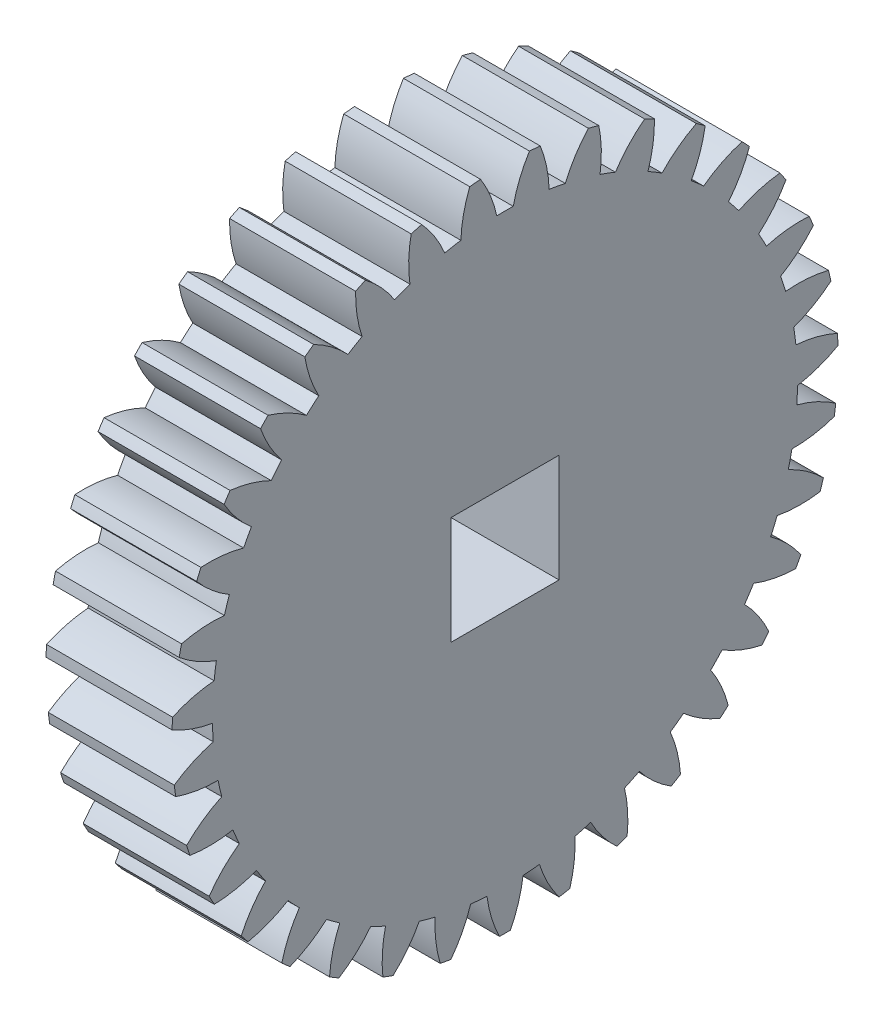
SolidWorks part; units mm, degrees
ref_plane "Plane1" through (0, 0, 0) normal (0, 0, 1) x (1, 0, 0)
ref_plane "Plane2" through (0, 0, 0) normal (0, 1, 0) x (1, 0, 0)
ref_plane "Plane3" through (0, 0, 0) normal (1, 0, 0) x (0, 0, -1)
sketch "HoldingSke" plane through (0, 0, 0) normal (0, 1, 0) x (1, 0, 0)
  line L0 (0, 0) -> (0.8192, -0.5736)
  line L1 (-15, 0) -> (100, 0) construction
  line L2 (0, 0) -> (-2.1039, 2.3779)
  line L3 (0, 0) -> (-11.863, 4.5341)
  line L4 (0, 0) -> (7.0742, 4.9534)
  line L5 (0, 0) -> (-46.8476, -17.4728)
  line L6 (0, 0) -> (-4.1448, -2.7965)
  line L7 (-2.1039, 2.3779) -> (8.6587, 51.2062)
  line L8 (-76.2, 54.61) -> (-75.2, 54.61)
  line L9 (-71.009, 38.7566) -> (-53.1078, 45.2721)
  line L10 (-76.2, 71.12) -> (104.1128, 71.12)
  line L11 (0, 0) -> (-5, 0)
  line L12 (-76.2, 101.6) -> (-76.162, 101.6)
  line L13 (24.9733, 27.94) -> (52.9518, 28.4284)
  line L14 (24.9733, 27.94) -> (24.9743, 27.94)
  line L15 (24.9733, 27.94) -> (100.4006, 29.5858)
  line L16 (-63.627, -1) -> (-12.827, -1)
  circle A0 centre (0, 0) radius 3
  circle A1 centre (0, 0) radius 16.249
  circle A2 centre (0, 0) radius 37.5
  circle A3 centre (0, 0) radius 3
  dimension "MHD" = 32.498
  dimension "Hub_dia" = 75
  dimension "Bore" = 6
  dimension "MBD" = 6
  dimension "Num_teeth" = 35
  dimension "Pitch_radius" = 180.3128
  dimension "Pitch" = 1
  dimension "Width" = 5
  dimension "Overall_len" = 50
  dimension "Show_teeth" = 35
  dimension "Thickness" = 5
  dimension "OAL" = 50.0004
  dimension "T_dim" = 1
  dimension "Ap" = 20
  dimension "H" = 19.05
  dimension "Backlash" = 0.038
  dimension "Addendum_fac" = 1
  dimension "Dedendum_fac" = 1.25
  dimension "Clearance_fac" = 0.25
  dimension "Dedendum_add" = 0.001
  dimension "Module" = 1
sketch "BasProSke" plane through (0, 0, 0) normal (0, 1, 0) x (1, 0, 0)
  line L0 (-10, 0) -> (60, 0) construction
  line L1 (0, 0) -> (0, 18.5)
  line L2 (0, 0) -> (7, 0)
  line L3 (7, 0) -> (7, 18.5)
  line L4 (7, 18.5) -> (0, 18.5)
  dimension "Diameter" = 37
  dimension "Thickness" = 7
revolve "Base-Revolve" add sketch "BasProSke" angle 360 about L0
sketch "TooCutSke" plane through (0, 0, 0) normal (1, 0, 0) x (0, 0, -1)
  line L1 (0, 0) -> (0, 107) construction
  line L2 (0, 0) -> (-0.8516, 17.4793) construction
  line L3 (0, 0) -> (-3.1347, 34.8297) construction
  line L4 (-0.8516, 17.4793) -> (-1.5674, 17.4148) construction
  arc A0 (0.4564, 16.2426) -> (-0.4564, 16.2426) centre (0, 0) ccw
  arc A1 (1.373, 18.4745) -> (-1.373, 18.4745) centre (0, 0) ccw
  circle A2 centre (0, 0) radius 17.5 construction
  circle A3 centre (0, 0) radius 16.4446 construction
  arc A4 (-0.4564, 16.2426) -> (-1.373, 18.4745) centre (-7.293, 14.739) ccw
  arc A5 (1.373, 18.4745) -> (0.4564, 16.2426) centre (7.293, 14.739) ccw
  dimension "Root_dia" = 32.498
  dimension "Overcut_dia" = 37.0508
  dimension "Pitch_dia" = 35
  dimension "Base_dia" = 32.8892
  dimension "Flank_rad" = 7
  dimension "Half_ang" = 5.143
  dimension "Half_CT" = 0.7186
extrude "ToothCut" cut sketch "TooCutSke" along normal through all
fillet "Breaks" [suppressed] radius 0.02
fillet "RootFillets" [suppressed] radius 0.251
pattern_circular "TeethCuts" count 35 every 10.286 about axis through (-10, 0, 0) along (1, 0, 0) of "ToothCut", "RootFillets", "Breaks"
sketch "HubNeaOneSke" plane through (0, 0, 0) normal (-1, 0, 0) x (0, 0, 1)
  circle A0 centre (0, 0) radius 16.249
  dimension "Diameter" = 32.498
extrude "HubNearOne" [suppressed] add sketch "HubNeaOneSke" along normal blind 43.0004
sketch "HubNeaBotSke" plane through (0, 0, 0) normal (-1, 0, 0) x (0, 0, 1)
  circle A0 centre (0, 0) radius 16.249
  dimension "Diameter" = 32.498
extrude "HubNearBoth" [suppressed] add sketch "HubNeaBotSke" along normal blind 21.5002
ref_plane "FarPln" through (7, 0, 0) normal (1, 0, 0) x (0, 0, -1)
sketch "HubFarSke" plane through (7, 0, 0) normal (1, 0, 0) x (0, 0, -1)
  circle A0 centre (0, 0) radius 16.249
  dimension "Diameter" = 32.498
extrude "HubFar" [suppressed] add sketch "HubFarSke" along normal blind 21.5002
sketch "BorSke" plane through (0, 0, 0) normal (1, 0, 0) x (0, 0, -1)
  circle A0 centre (0, 0) radius 1.5
  dimension "Diameter" = 3
extrude "Bore" cut sketch "BorSke" along normal mid plane 100.0007
sketch "KeySke" plane through (0, 0, 0) normal (1, 0, 0) x (0, 0, -1)
  line L0 (-1, 0) -> (-1, 4)
  line L1 (-1, 4) -> (1, 4)
  line L2 (1, 4) -> (1, 0)
  line L3 (0, 0) -> (0, 34) construction
  line L4 (-1, 0) -> (1, 0)
  dimension "Offset" = 4
  dimension "Width" = 2
extrude "Keyway" [suppressed] cut sketch "KeySke" along normal mid plane 100.0007
pattern_circular "Keyway2" [suppressed] count 2 every 90 about axis through (-10, 0, 0) along (1, 0, 0)
sketch "Sketch1" plane through (7, 0, 0) normal (1, 0, 0) x (0, 0, -1)
  line L1 (-3, -3) -> (3, -3)
  line L2 (-3, -3) -> (-3, 3)
  line L3 (-3, 3) -> (3, 3)
  line L4 (3, -3) -> (3, 3)
  line L5 (-3, -3) -> (3, 3) construction
  line L6 (-3, 3) -> (3, -3) construction
  circle A0 centre (0, 0) radius 1.5 construction
  point P0 (0, 0)
  dimension "D1" = 0
  dimension "D2" = 6
  dimension "D3" = 6
extrude "Cut-Extrude1" cut sketch "Sketch1" against normal blind 10
equation "' \"Module@HoldingSke\" = 6.35"
equation "' \"Num_teeth@HoldingSke\" = 12"
equation "' \"Ap@HoldingSke\" =  20"
equation "' \"Width@HoldingSke\" = 0.5 * 25.4"
equation "' \"Hub_dia@HoldingSke\"= 1 * 25.4"
equation "' \"Overall_len@HoldingSke\" = 1.0 * 25.4"
equation "' \"Bore@HoldingSke\" = 0.75 * 25.4"
equation "' \"T_dim@HoldingSke\" = 0.1 * 25.4"
equation "' \"Width@KeySke\" = 0.25 * 25.4"
equation "' \"Show_teeth@HoldingSke\" = 13"
equation "' \"Backlash@HoldingSke\" = 0.009 * 25.4"
equation "' \"Addendum_fac@HoldingSke\" = 1.0"
equation "' \"Dedendum_fac@HoldingSke\" = 1.25"
equation "' \"Dedendum_add@HoldingSke\" = 0.00005 * 25.4"
equation "' \"Clearance_fac@HoldingSke\" = 0.25"
equation "\"Pitch@HoldingSke\" = 1 / \"Module@HoldingSke\""
equation "\"Overcut_dia@TooCutSke\" = (\"Num_teeth@HoldingSke\" + 2 * \"Addendum_fac@HoldingSke\") / \"Pitch@HoldingSke\" + 0.002 * 25.4"
equation "\"Pitch_dia@TooCutSke\" = \"Num_teeth@HoldingSke\" / \"Pitch@HoldingSke\""
equation "\"Base_dia@TooCutSke\" = \"Num_teeth@HoldingSke\" / \"Pitch@HoldingSke\" * cos((\"Ap@HoldingSke\"  * 3.14159265 / 180))"
equation "\"Root_dia@TooCutSke\" = (\"Num_teeth@HoldingSke\" + 2) / \"Pitch@HoldingSke\" - 2 * (\"Addendum_fac@HoldingSke\" + \"Dedendum_fac@HoldingSke\") / \"Pitch@HoldingSke\" - \"Dedendum_add@HoldingSke\" * 2"
equation "\"Half_ang@TooCutSke\" = 180 / \"Num_teeth@HoldingSke\""
equation "\"Half_CT@TooCutSke\" = \"Num_teeth@HoldingSke\" / \"Pitch@HoldingSke\" * sin((3.14159265 / 2 / \"Num_teeth@HoldingSke\")) / 2 - 7 * \"Backlash@HoldingSke\" / 4"
equation "\"Flank_rad@TooCutSke\" = \"Num_teeth@HoldingSke\" / \"Pitch@HoldingSke\" / 5"
equation "\"Radius@RootFillets\" = \"Clearance_fac@HoldingSke\" / \"Pitch@HoldingSke\" + \"Dedendum_add@HoldingSke\""
equation "\"Break_rad@Breaks\" = 0.02 / \"Pitch@HoldingSke\""
equation "\"Thickness@HoldingSke\" = \"Width@HoldingSke\""
equation "\"OAL@HoldingSke\" = \"Thickness@HoldingSke\""
equation "\"MHD@HoldingSke\" = (\"Num_teeth@HoldingSke\" + 2) / \"Pitch@HoldingSke\" - 2 * (\"Addendum_fac@HoldingSke\" + \"Dedendum_fac@HoldingSke\")  / \"Pitch@HoldingSke\" - \"Dedendum_add@HoldingSke\" * 2"
equation "\"MBD@HoldingSke\" = (\"Num_teeth@HoldingSke\" + 2) / \"Pitch@HoldingSke\" - 2 * (\"Addendum_fac@HoldingSke\" + \"Dedendum_fac@HoldingSke\")  / \"Pitch@HoldingSke\" - \"Dedendum_add@HoldingSke\" * 2 - 0.002 * 25.4"
equation "\"MHD@HoldingSke\" = ((sgn( \"MHD@HoldingSke\" - \"Hub_dia@HoldingSke\" )-1)*( \"MHD@HoldingSke\" - \"Hub_dia@HoldingSke\" ))/-2+ \"Hub_dia@HoldingSke\""
equation "\"MBD@HoldingSke\" = ((sgn( \"MBD@HoldingSke\" - \"Bore@HoldingSke\" )-1)*( \"MBD@HoldingSke\" - \"Bore@HoldingSke\" ))/-2+ \"Bore@HoldingSke\""
equation "\"OAL@HoldingSke\" = ((sgn( \"OAL@HoldingSke\" - \"Overall_len@HoldingSke\" )+1)*( \"OAL@HoldingSke\" - \"Overall_len@HoldingSke\" ))/2 + \"Overall_len@HoldingSke\" + 0.000002 * 25.4"
equation "\"Num_teeth@TeethCuts\" = int( \"Show_teeth@HoldingSke\" ) + 1"
equation "\"Num_teeth@TeethCuts\" = ((sgn( \"Num_teeth@TeethCuts\" - \"Num_teeth@HoldingSke\" )-1)*( \"Num_teeth@TeethCuts\" - \"Num_teeth@HoldingSke\" ))/-2+ \"Num_teeth@HoldingSke\""
equation "\"Num_teeth@TeethCuts\" = ((sgn( \"Num_teeth@TeethCuts\" - 2.0)+1)*( \"Num_teeth@TeethCuts\" - 2.0))/2 +2.0"
equation "\"Angle@TeethCuts\" = 360.0 / \"Num_teeth@HoldingSke\""
equation "\"Diameter@BasProSke\" = (\"Num_teeth@HoldingSke\" + 2 * \"Addendum_fac@HoldingSke\") / \"Pitch@HoldingSke\""
equation "\"Thickness@BasProSke\"=7mm"
equation "' \"Fillet_rad@BasProSke\" =  \"Thickness@HoldingSke\" * 0.05"
equation "\"MHD@HoldingSke\" = ((sgn( \"MHD@HoldingSke\" - \"Root_dia@TooCutSke\" )-1)*( \"MHD@HoldingSke\" - \"Root_dia@TooCutSke\" ))/-2+ \"Root_dia@TooCutSke\""
equation "\"Diameter@HubNeaOneSke\" = \"MHD@HoldingSke\""
equation "\"Length@HubNearOne\" = \"OAL@HoldingSke\" - \"Thickness@BasProSke\""
equation "\"Diameter@HubNeaBotSke\" = \"MHD@HoldingSke\""
equation "\"Length@HubNearBoth\" = ( \"OAL@HoldingSke\" - \"Thickness@BasProSke\" ) / 2.0"
equation "\"Thickness@FarPln\"= 7mm"
equation "\"Diameter@HubFarSke\" = \"MHD@HoldingSke\""
equation "\"Length@HubFar\" = ( \"OAL@HoldingSke\" - \"Thickness@BasProSke\" ) / 2.0"
equation "\"Diameter@BorSke\"=3"
equation "\"D1@Bore\" = \"OAL@HoldingSke\" * 2.0"
equation "\"D1@Keyway\" = \"OAL@HoldingSke\" * 2.0"
equation "\"Offset@KeySke\" = \"T_dim@HoldingSke\" + \"MBD@HoldingSke\" / 2.0"
